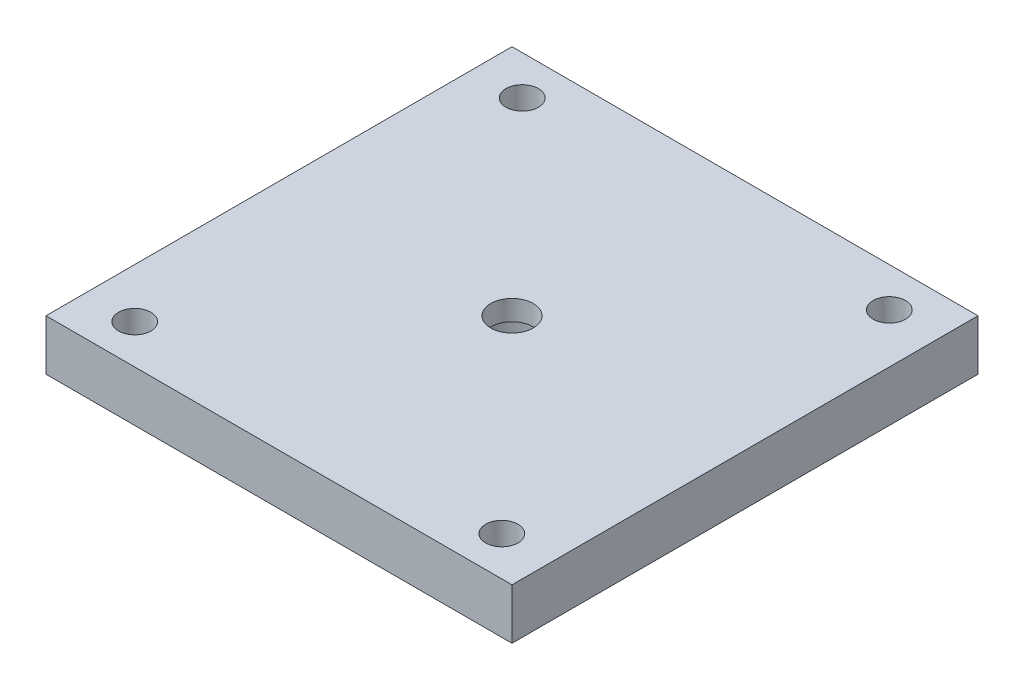
SolidWorks part; units mm, degrees
ref_plane "Front Plane" through (0, 0, 0) normal (0, 0, 1) x (1, 0, 0)
ref_plane "Top Plane" through (0, 0, 0) normal (0, 1, 0) x (1, 0, 0)
ref_plane "Right Plane" through (0, 0, 0) normal (1, 0, 0) x (0, 0, -1)
sketch "Sketch1" plane through (0, 0, 0) normal (0, 1, 0) x (1, 0, 0)
  line L1 (-23, 23) -> (23, 23)
  line L2 (-23, 23) -> (-23, -23)
  line L3 (-23, -23) -> (23, -23)
  line L4 (23, 23) -> (23, -23)
  line L5 (-23, 23) -> (23, -23) construction
  line L6 (-23, -23) -> (23, 23) construction
  point P0 (0, 0)
extrude "Boss-Extrude1" add sketch "Sketch1" along normal blind 5
sketch "Sketch3" plane through (0, 0, 0) normal (0, 1, 0) x (1, 0, 0)
  circle A0 centre (0, 0) radius 4.1
extrude "Cut-Extrude2" cut sketch "Sketch3" along normal blind 3
sketch "Sketch4" plane through (0, 0, 0) normal (0, 1, 0) x (1, 0, 0)
  circle A0 centre (0, 0) radius 2.1
extrude "Cut-Extrude3" cut sketch "Sketch4" along normal through all
sketch "Sketch5" plane through (0, 0, 0) normal (0, 1, 0) x (1, 0, 0)
  line L0 (0, 0) -> (7.5, 0) construction
  line L1 (0, 0) -> (-7.5, 0) construction
  line L3 (5, 2.5) -> (10, 2.5)
  line L4 (5, 2.5) -> (5, -2.5)
  line L5 (5, -2.5) -> (10, -2.5)
  line L6 (10, 2.5) -> (10, -2.5)
  line L7 (5, 2.5) -> (10, -2.5) construction
  line L8 (5, -2.5) -> (10, 2.5) construction
  line L9 (-10, -2.5) -> (-5, -2.5)
  line L10 (-10, -2.5) -> (-10, 2.5)
  line L11 (-10, 2.5) -> (-5, 2.5)
  line L12 (-5, -2.5) -> (-5, 2.5)
  line L13 (-10, -2.5) -> (-5, 2.5) construction
  line L14 (-10, 2.5) -> (-5, -2.5) construction
extrude "Boss-Extrude2" add sketch "Sketch5" against normal blind 2
ref_plane "Plane1" through (0, -2, 0) normal (0, -1, 0) x (-1, 0, 0)
sketch "Sketch6" plane through (0, -2, 0) normal (0, -1, 0) x (-1, 0, 0)
  line L0 (0, 0) -> (-7.5, 0) construction
  line L1 (0, 0) -> (7.5, 0) construction
  circle A0 centre (7.5, 0) radius 1
  circle A1 centre (-7.5, 0) radius 1
extrude "Cut-Extrude4" cut sketch "Sketch6" against normal blind 5
sketch "Sketch7" plane through (0, 0, 0) normal (0, 1, 0) x (1, 0, 0)
  line L0 (0, 0) -> (-18.12, 0) construction
  line L1 (-18.12, 0) -> (-18.12, -19.125) construction
  line L2 (-18.12, -19.125) -> (18.12, -19.125) construction
  line L3 (18.12, -19.125) -> (18.12, 19.125) construction
  line L4 (18.12, 19.125) -> (-18.12, 19.125) construction
  circle A0 centre (-18.12, -19.125) radius 1.6
  circle A1 centre (18.12, -19.125) radius 1.6
  circle A2 centre (18.12, 19.125) radius 1.6
  circle A3 centre (-18.12, 19.125) radius 1.6
extrude "Cut-Extrude5" cut sketch "Sketch7" along normal blind 5
